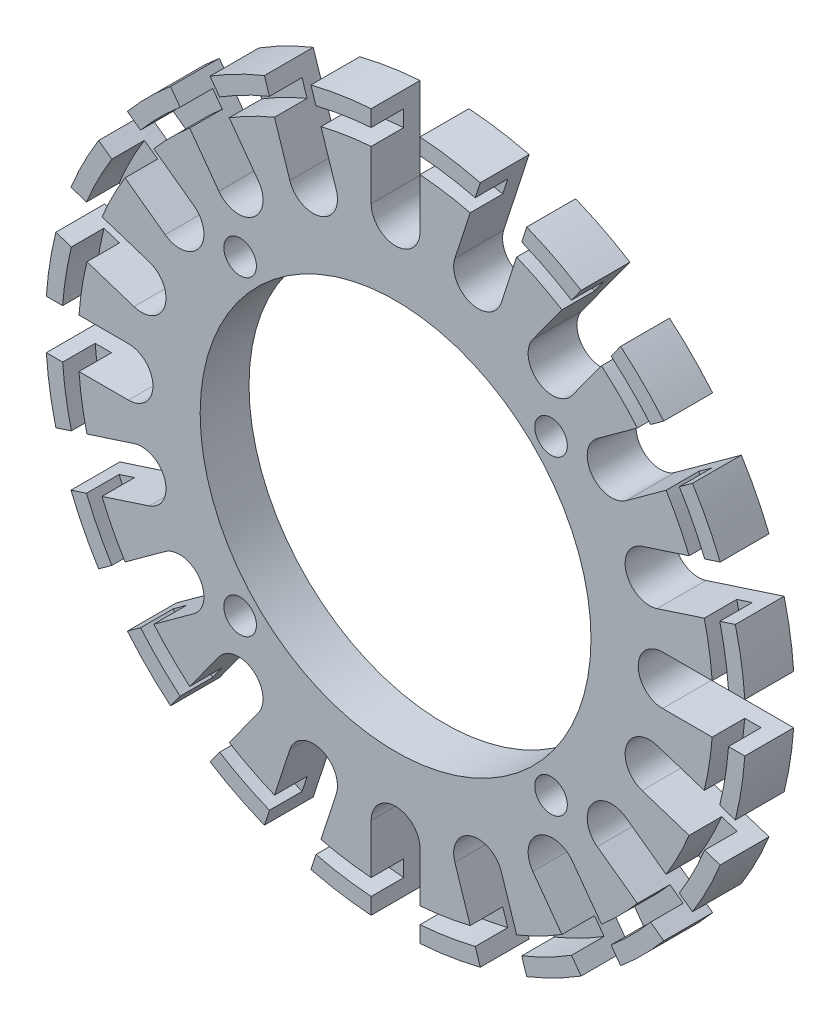
SolidWorks part; units mm, degrees
ref_plane "Front" through (0, 0, 0) normal (0, 0, 1) x (1, 0, 0)
ref_plane "Top" through (0, 0, 0) normal (0, 1, 0) x (1, 0, 0)
ref_plane "Right" through (0, 0, 0) normal (1, 0, 0) x (0, 0, -1)
sketch "Sketch1" plane through (0, 0, 0) normal (0, 0, 1) x (1, 0, 0)
  line L2 (-1.5, 16.4) -> (-1.5, 21.4476)
  line L5 (1.5, 21.4476) -> (1.5, 16.4)
  line L6 (8.0543, 19.9344) -> (6.4945, 15.1338)
  line L7 (3.6413, 16.0609) -> (5.2011, 20.8614)
  line L8 (13.8201, 16.4698) -> (10.8532, 12.3862)
  line L9 (8.4262, 14.1496) -> (11.3931, 18.2332)
  line L10 (18.2332, 11.3931) -> (14.1496, 8.4262)
  line L11 (12.3862, 10.8532) -> (16.4698, 13.8201)
  line L12 (20.8614, 5.2011) -> (16.0609, 3.6413)
  line L13 (15.1338, 6.4945) -> (19.9344, 8.0543)
  line L14 (21.4476, -1.5) -> (16.4, -1.5)
  line L15 (16.4, 1.5) -> (21.4476, 1.5)
  line L16 (19.9344, -8.0543) -> (15.1338, -6.4945)
  line L17 (16.0609, -3.6413) -> (20.8614, -5.2011)
  line L18 (16.4698, -13.8201) -> (12.3862, -10.8532)
  line L19 (14.1496, -8.4262) -> (18.2332, -11.3931)
  line L20 (11.3931, -18.2332) -> (8.4262, -14.1496)
  line L21 (10.8532, -12.3862) -> (13.8201, -16.4698)
  line L22 (5.2011, -20.8614) -> (3.6413, -16.0609)
  line L23 (6.4945, -15.1338) -> (8.0543, -19.9344)
  line L24 (-1.5, -21.4476) -> (-1.5, -16.4)
  line L25 (1.5, -16.4) -> (1.5, -21.4476)
  line L26 (-8.0543, -19.9344) -> (-6.4945, -15.1338)
  line L27 (-3.6413, -16.0609) -> (-5.2011, -20.8614)
  line L28 (-13.8201, -16.4698) -> (-10.8532, -12.3862)
  line L29 (-8.4262, -14.1496) -> (-11.3931, -18.2332)
  line L30 (-18.2332, -11.3931) -> (-14.1496, -8.4262)
  line L31 (-12.3862, -10.8532) -> (-16.4698, -13.8201)
  line L32 (-20.8614, -5.2011) -> (-16.0609, -3.6413)
  line L33 (-15.1338, -6.4945) -> (-19.9344, -8.0543)
  line L34 (-21.4476, 1.5) -> (-16.4, 1.5)
  line L35 (-16.4, -1.5) -> (-21.4476, -1.5)
  line L36 (-19.9344, 8.0543) -> (-15.1338, 6.4945)
  line L37 (-16.0609, 3.6413) -> (-20.8614, 5.2011)
  line L38 (-16.4698, 13.8201) -> (-12.3862, 10.8532)
  line L39 (-14.1496, 8.4262) -> (-18.2332, 11.3931)
  line L40 (-11.3931, 18.2332) -> (-8.4262, 14.1496)
  line L41 (-10.8532, 12.3862) -> (-13.8201, 16.4698)
  line L42 (-5.2011, 20.8614) -> (-3.6413, 16.0609)
  line L43 (-6.4945, 15.1338) -> (-8.0543, 19.9344)
  circle A0 centre (0, 0) radius 12
  circle A2 centre (0, 13.5) radius 1
  circle A5 centre (13.5, 0) radius 1
  circle A6 centre (0, -13.5) radius 1
  circle A7 centre (-13.5, 0) radius 1
  arc A11 (-1.5, 16.4) -> (1.5, 16.4) centre (0, 16.4) ccw
  arc A12 (-1.5, 21.4476) -> (-5.2011, 20.8614) centre (0, 0) ccw
  arc A13 (3.6413, 16.0609) -> (6.4945, 15.1338) centre (5.0679, 15.5973) ccw
  arc A14 (8.4262, 14.1496) -> (10.8532, 12.3862) centre (9.6397, 13.2679) ccw
  arc A15 (12.3862, 10.8532) -> (14.1496, 8.4262) centre (13.2679, 9.6397) ccw
  arc A16 (15.1338, 6.4945) -> (16.0609, 3.6413) centre (15.5973, 5.0679) ccw
  arc A17 (16.4, 1.5) -> (16.4, -1.5) centre (16.4, 0) ccw
  arc A18 (16.0609, -3.6413) -> (15.1338, -6.4945) centre (15.5973, -5.0679) ccw
  arc A19 (14.1496, -8.4262) -> (12.3862, -10.8532) centre (13.2679, -9.6397) ccw
  arc A20 (10.8532, -12.3862) -> (8.4262, -14.1496) centre (9.6397, -13.2679) ccw
  arc A21 (6.4945, -15.1338) -> (3.6413, -16.0609) centre (5.0679, -15.5973) ccw
  arc A22 (1.5, -16.4) -> (-1.5, -16.4) centre (0, -16.4) ccw
  arc A23 (-3.6413, -16.0609) -> (-6.4945, -15.1338) centre (-5.0679, -15.5973) ccw
  arc A24 (-8.4262, -14.1496) -> (-10.8532, -12.3862) centre (-9.6397, -13.2679) ccw
  arc A25 (-12.3862, -10.8532) -> (-14.1496, -8.4262) centre (-13.2679, -9.6397) ccw
  arc A26 (-15.1338, -6.4945) -> (-16.0609, -3.6413) centre (-15.5973, -5.0679) ccw
  arc A27 (-16.4, -1.5) -> (-16.4, 1.5) centre (-16.4, 0) ccw
  arc A28 (-16.0609, 3.6413) -> (-15.1338, 6.4945) centre (-15.5973, 5.0679) ccw
  arc A29 (-14.1496, 8.4262) -> (-12.3862, 10.8532) centre (-13.2679, 9.6397) ccw
  arc A30 (-10.8532, 12.3862) -> (-8.4262, 14.1496) centre (-9.6397, 13.2679) ccw
  arc A31 (-6.4945, 15.1338) -> (-3.6413, 16.0609) centre (-5.0679, 15.5973) ccw
  arc A32 (-8.0543, 19.9344) -> (-11.3931, 18.2332) centre (0, 0) ccw
  arc A33 (5.2011, 20.8614) -> (1.5, 21.4476) centre (0, 0) ccw
  arc A34 (11.3931, 18.2332) -> (8.0543, 19.9344) centre (0, 0) ccw
  arc A35 (16.4698, 13.8201) -> (13.8201, 16.4698) centre (0, 0) ccw
  arc A36 (19.9344, 8.0543) -> (18.2332, 11.3931) centre (0, 0) ccw
  arc A37 (21.4476, 1.5) -> (20.8614, 5.2011) centre (0, 0) ccw
  arc A38 (20.8614, -5.2011) -> (21.4476, -1.5) centre (0, 0) ccw
  arc A39 (18.2332, -11.3931) -> (19.9344, -8.0543) centre (0, 0) ccw
  arc A40 (13.8201, -16.4698) -> (16.4698, -13.8201) centre (0, 0) ccw
  arc A41 (8.0543, -19.9344) -> (11.3931, -18.2332) centre (0, 0) ccw
  arc A42 (1.5, -21.4476) -> (5.2011, -20.8614) centre (0, 0) ccw
  arc A43 (-5.2011, -20.8614) -> (-1.5, -21.4476) centre (0, 0) ccw
  arc A44 (-11.3931, -18.2332) -> (-8.0543, -19.9344) centre (0, 0) ccw
  arc A45 (-16.4698, -13.8201) -> (-13.8201, -16.4698) centre (0, 0) ccw
  arc A46 (-19.9344, -8.0543) -> (-18.2332, -11.3931) centre (0, 0) ccw
  arc A47 (-21.4476, -1.5) -> (-20.8614, -5.2011) centre (0, 0) ccw
  arc A48 (-20.8614, 5.2011) -> (-21.4476, 1.5) centre (0, 0) ccw
  arc A49 (-13.8201, 16.4698) -> (-16.4698, 13.8201) centre (0, 0) ccw
  arc A50 (-18.2332, 11.3931) -> (-19.9344, 8.0543) centre (0, 0) ccw
  dimension "D1" = 4
  dimension "D2" = 20
extrude "Boss-Extrude1" add sketch "Sketch1" along normal blind 3
sketch "Sketch2" plane through (0, 0, 3) normal (0, 0, 1) x (1, 0, 0)
  circle A0 centre (0, 0) radius 19.5
  circle A1 centre (0, 0) radius 20.5
extrude "Cut-Extrude1" cut sketch "Sketch2" against normal blind 2
sketch "Sketch3" plane through (0, 0, 3) normal (0, 0, 1) x (1, 0, 0)
  circle A0 centre (0, 0) radius 12
  circle A1 centre (0, 0) radius 14.9
extrude "Boss-Extrude2" add sketch "Sketch3" against normal up to surface (3 mm away) up to face at (0, 0, 0)
sketch "Sketch4" plane through (0, 0, 3) normal (0, 0, 1) x (1, 0, 0)
  circle A1 centre (9.5459, 9.5459) radius 1
  circle A2 centre (9.5459, -9.5459) radius 1
  circle A3 centre (-9.5459, -9.5459) radius 1
  circle A4 centre (-9.5459, 9.5459) radius 1
  dimension "D1" = 4
extrude "Cut-Extrude3" cut sketch "Sketch4" against normal blind 10
